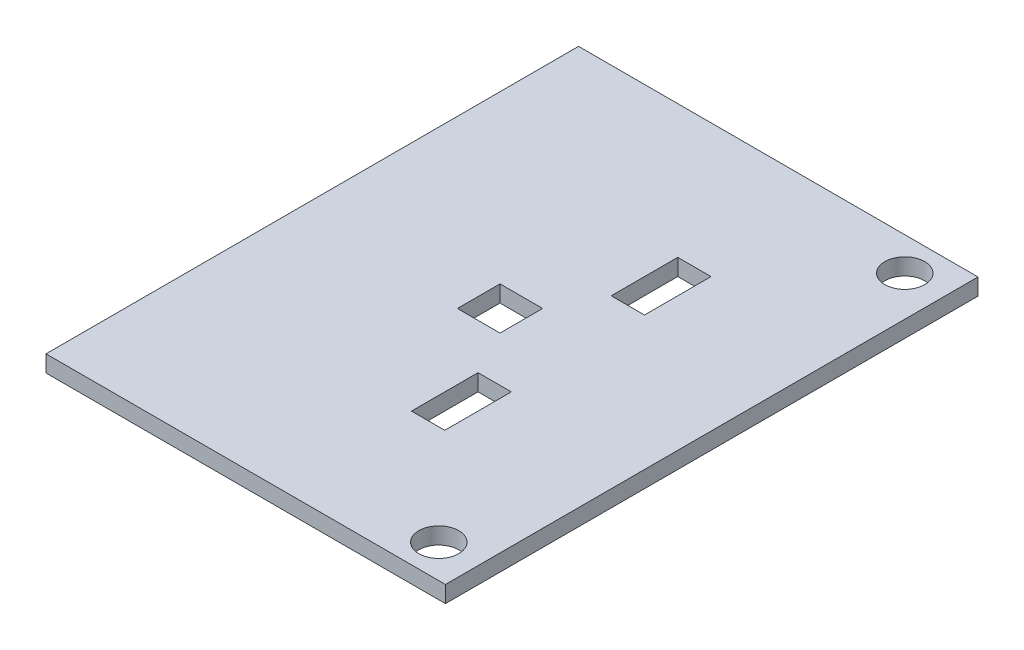
SolidWorks part; units mm, degrees
ref_plane "Front Plane" through (0, 0, 0) normal (0, 0, 1) x (1, 0, 0)
ref_plane "Top Plane" through (0, 0, 0) normal (0, 1, 0) x (1, 0, 0)
ref_plane "Right Plane" through (0, 0, 0) normal (1, 0, 0) x (0, 0, -1)
sketch "Sketch1" plane through (0, 0, 0) normal (0, 1, 0) x (1, 0, 0)
  line L1 (0, 0) -> (76.2, 0)
  line L2 (0, 0) -> (0, 101.6)
  line L3 (0, 101.6) -> (76.2, 101.6)
  line L4 (76.2, 0) -> (76.2, 101.6)
  dimension "D1" = 76.2
  dimension "D2" = 101.6
extrude "Boss-Extrude1" add sketch "Sketch1" along normal blind 3.175
sketch "Sketch2" plane through (0, 3.175, 0) normal (0, 1, 0) x (1, 0, 0)
  line L0 (68.58, 0) -> (68.58, 101.6) construction
  line L1 (0, 0) -> (76.2, 0) construction
  line L2 (76.2, 101.6) -> (0, 101.6) construction
  line L3 (0, 6.35) -> (76.2, 6.35) construction
  line L4 (0, 101.6) -> (0, 0) construction
  line L5 (76.2, 0) -> (76.2, 101.6) construction
  line L6 (0, 95.25) -> (76.2, 95.25) construction
  line L7 (38.1, 95.25) -> (38.1, 6.35) construction
  line L8 (47.498, 69.85) -> (47.498, 31.75) construction
  line L9 (44.323, 76.2) -> (50.673, 76.2)
  line L10 (44.323, 76.2) -> (44.323, 63.5)
  line L11 (44.323, 63.5) -> (50.673, 63.5)
  line L12 (50.673, 76.2) -> (50.673, 63.5)
  line L13 (44.323, 76.2) -> (50.673, 63.5) construction
  line L14 (44.323, 63.5) -> (50.673, 76.2) construction
  line L15 (44.323, 38.1) -> (50.673, 38.1)
  line L16 (44.323, 38.1) -> (44.323, 25.4)
  line L17 (44.323, 25.4) -> (50.673, 25.4)
  line L18 (50.673, 38.1) -> (50.673, 25.4)
  line L19 (44.323, 38.1) -> (50.673, 25.4) construction
  line L20 (44.323, 25.4) -> (50.673, 38.1) construction
  line L21 (0, 50.8) -> (76.2, 50.8) construction
  line L23 (31.75, 54.864) -> (39.878, 54.864)
  line L24 (31.75, 54.864) -> (31.75, 46.736)
  line L25 (31.75, 46.736) -> (39.878, 46.736)
  line L26 (39.878, 54.864) -> (39.878, 46.736)
  line L27 (31.75, 54.864) -> (39.878, 46.736) construction
  line L28 (31.75, 46.736) -> (39.878, 54.864) construction
  circle A0 centre (68.58, 95.25) radius 3.81
  circle A1 centre (68.58, 6.35) radius 3.81
  point P18 (47.498, 69.85)
  point P25 (47.498, 31.75)
  point P32 (35.814, 50.8)
  dimension "D4" = 7.62
  dimension "D5" = 25.4
  dimension "D1" = 6.35
  dimension "D2" = 6.35
  dimension "D3" = 7.62
  dimension "D6" = 6.35
  dimension "D7" = 6.35
  dimension "D8" = 12.7
  dimension "D9" = 12.7
  dimension "D10" = 12.7
  dimension "D11" = 8.128
  dimension "D12" = 10.795
  dimension "D13" = 31.75
  dimension "D14" = 8.128
extrude "Cut-Extrude1" cut sketch "Sketch2" against normal through all
